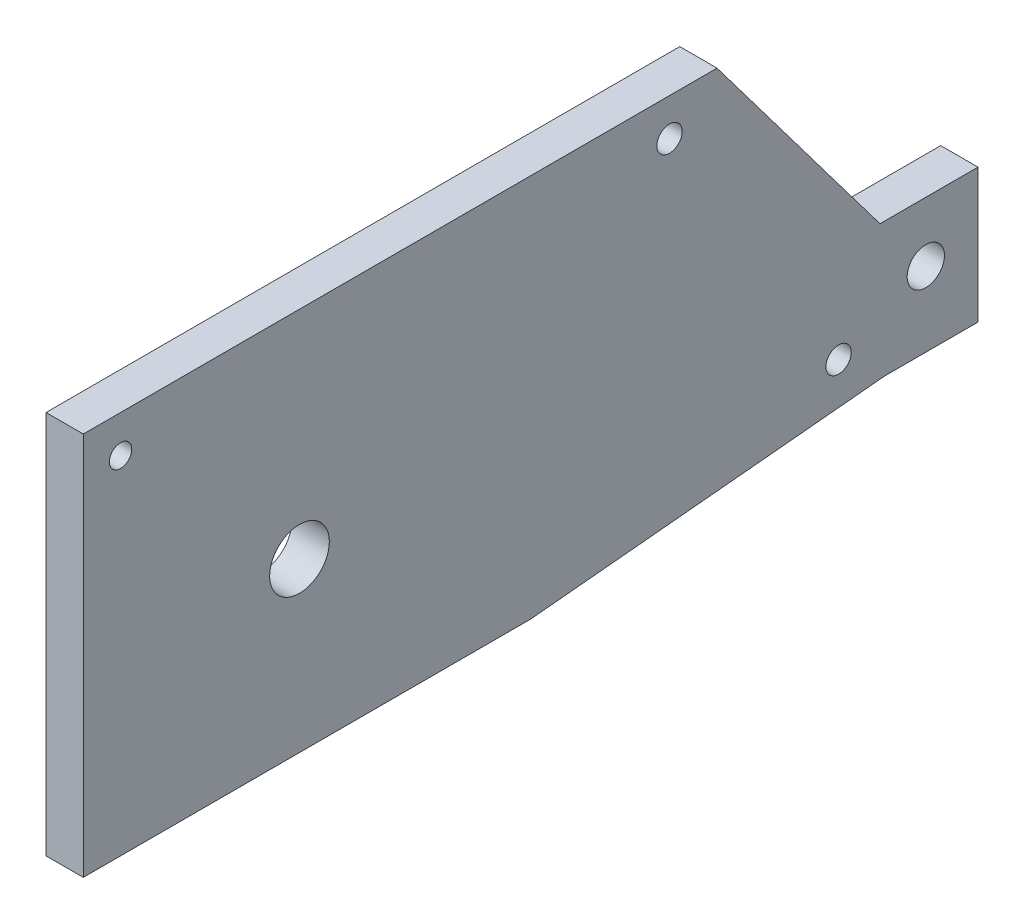
SolidWorks part; units mm, degrees
material "Hexcel AS4C (3000 filamentos)"
ref_plane "Alzado" through (0, 0, 0) normal (0, 0, 1) x (1, 0, 0)
ref_plane "Planta" through (0, 0, 0) normal (0, 1, 0) x (1, 0, 0)
ref_plane "Vista lateral" through (0, 0, 0) normal (1, 0, 0) x (0, 0, -1)
sketch "Croquis1" plane through (0, 0, 0) normal (1, 0, 0) x (0, 0, -1)
  line L1 (60, -25.75) -> (-60, -25.75)
  line L2 (60, -25.75) -> (60, 25.75)
  line L3 (60, 25.75) -> (-60, 25.75)
  line L4 (-60, -25.75) -> (-60, 25.75)
  line L5 (60, -25.75) -> (-60, 25.75) construction
  line L6 (60, 25.75) -> (-60, -25.75) construction
  point P0 (0, 0)
  dimension "D1" = 120
  dimension "D2" = 51.5
extrude "Saliente-Extruir1" add sketch "Croquis1" along normal blind 5
sketch "Croquis2" plane through (5, 0, 0) normal (1, 0, 0) x (0, 0, -1)
  line L0 (-60, 25.75) -> (25, 25.75) construction
  line L1 (60, 25.75) -> (-60, 25.75) construction
  line L2 (60, 25.75) -> (60, -3.25) construction
  line L3 (60, -25.75) -> (60, 25.75) construction
  line L6 (60, -3.25) -> (46.8531, -3.25) construction
  line L7 (25, 25.75) -> (46.8531, -3.25)
  line L8 (46.8531, -3.25) -> (60, -3.25)
  line L9 (60, -3.25) -> (60, 25.75)
  line L10 (25, 25.75) -> (60, 25.75)
  dimension "D1" = 85
  dimension "D2" = 29
  dimension "D4" = 127
extrude "Cortar-Extruir1" cut sketch "Croquis2" against normal up to next
sketch "Croquis3" plane through (5, 0, 0) normal (1, 0, 0) x (0, 0, -1)
  line L0 (-60, 25.75) -> (-55, 25.75) construction
  line L1 (25, 25.75) -> (-60, 25.75) construction
  line L2 (-55, 25.75) -> (-55, 20.75) construction
  line L3 (-55, 20.75) -> (-31, 20.75) construction
  line L4 (-31, 20.75) -> (-31, -3.25) construction
  circle A0 centre (-55, 20.75) radius 1.5
  circle A1 centre (-31, -3.25) radius 4
  dimension "D3" = 3
  dimension "D4" = 8
  dimension "D1" = 5
  dimension "D2" = 5
extrude "Cortar-Extruir2" cut sketch "Croquis3" against normal up to next
sketch "Croquis4" plane through (0, 0, 0) normal (-1, 0, 0) x (0, 0, 1)
  circle A0 centre (-18.6237, 20.75) radius 1.7
  circle A1 centre (-41.3015, -16.25) radius 1.7
extrude "Cortar-Extruir3" cut sketch "Croquis4" against normal up to next
sketch "Croquis5" plane through (5, 0, 0) normal (1, 0, 0) x (0, 0, -1)
  line L0 (60, -25.75) -> (60, -21.25) construction
  line L1 (60, -25.75) -> (60, -3.25) construction
  line L2 (47.5, -21.25) -> (0, -25.75)
  line L3 (60, -25.75) -> (47.5, -25.75)
  line L4 (60, -25.75) -> (60, -21.25)
  line L5 (60, -21.25) -> (47.5, -21.25)
  line L7 (-60, -25.75) -> (60, -25.75) construction
  line L8 (0, -25.75) -> (47.5, -25.75)
  dimension "D1" = 12.5
extrude "Cortar-Extruir4" cut sketch "Croquis5" against normal up to next contours L2 L8 L3 L4 L5
sketch "Croquis9" plane through (5, 0, 0) normal (1, 0, 0) x (0, 0, -1)
  line L0 (60, -3.25) -> (60, -11.25) construction
  line L1 (60, -21.25) -> (60, -3.25) construction
  line L2 (60, -11.25) -> (53, -11.25) construction
  circle A0 centre (53, -11.25) radius 2.5
  dimension "D3" = 5
  dimension "D1" = 8
  dimension "D2" = 7
extrude "Cortar-Extruir8" cut sketch "Croquis9" against normal blind 10
